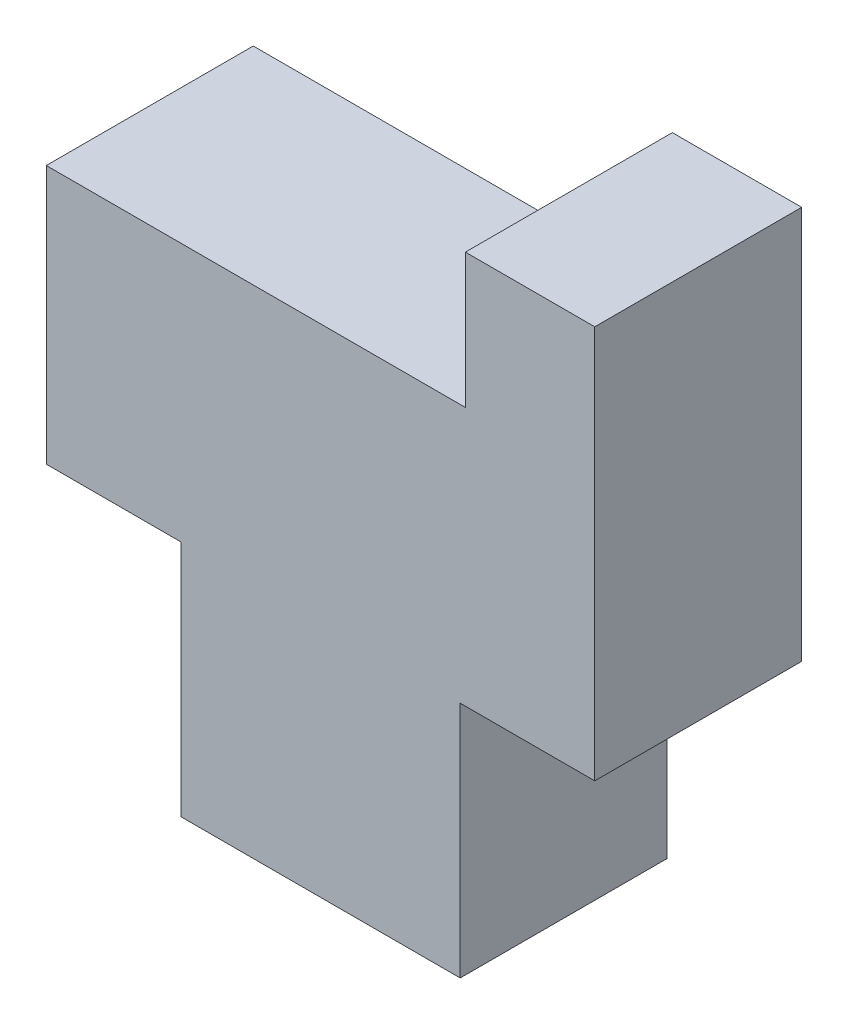
SolidWorks part; units mm, degrees
ref_plane "Front Plane" through (0, 0, 0) normal (0, 0, 1) x (1, 0, 0)
ref_plane "Top Plane" through (0, 0, 0) normal (0, 1, 0) x (1, 0, 0)
ref_plane "Right Plane" through (0, 0, 0) normal (1, 0, 0) x (0, 0, -1)
sketch "Sketch1" plane through (0, 0, 0) normal (0, 0, 1) x (1, 0, 0)
  line L0 (0, 0) -> (5.4, 0)
  line L1 (0, 0) -> (0, 4.6)
  line L2 (5.4, 0) -> (5.4, 4.6)
  line L3 (5.4, 4.6) -> (8, 4.6)
  line L4 (-2.6, 9.6) -> (5.5, 9.6)
  line L5 (5.5, 9.6) -> (5.5, 12.2)
  line L6 (5.5, 12.2) -> (8, 12.2)
  line L7 (8, 12.2) -> (8, 4.6)
  line L8 (0, 4.6) -> (-2.6, 4.6)
  line L9 (-2.6, 4.6) -> (-2.6, 9.6)
  dimension "D1" = 5.4
  dimension "D2" = 8
  dimension "D3" = 7.6
  dimension "D4" = 2.5
  dimension "D5" = 9.6
extrude "Boss-Extrude1" add sketch "Sketch1" along normal blind 4
equation "\"D1@Sketch1\"= 6 - \"tol2@parametersSketch@prostheticParameters.SLDPRT\" * 2"
